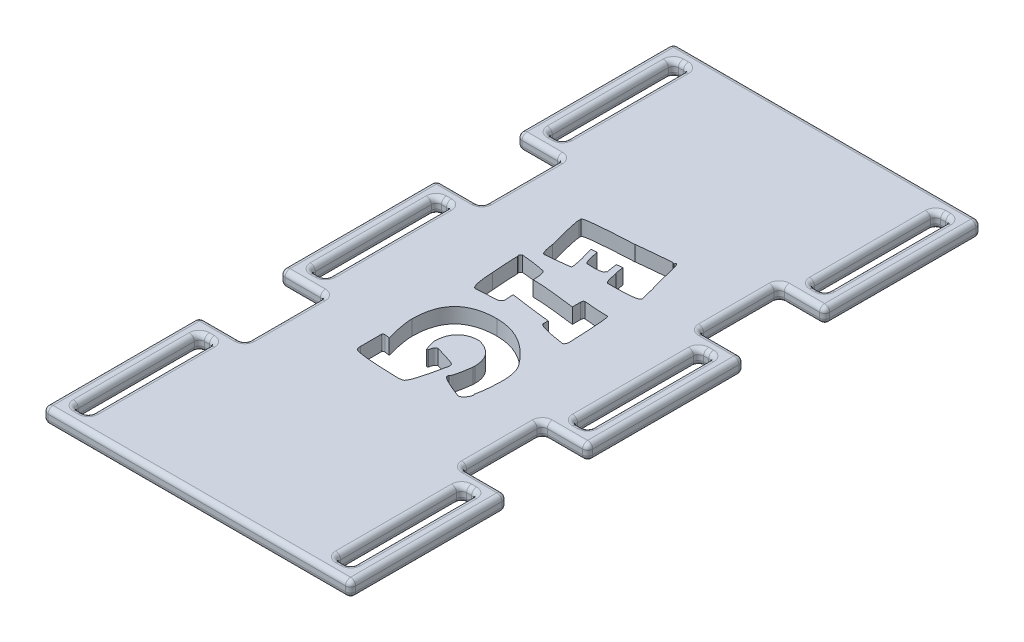
SolidWorks part; units mm, degrees
ref_plane "Front Plane" through (0, 0, 0) normal (0, 0, 1) x (1, 0, 0)
ref_plane "Top Plane" through (0, 0, 0) normal (0, 1, 0) x (1, 0, 0)
ref_plane "Right Plane" through (0, 0, 0) normal (1, 0, 0) x (0, 0, -1)
sketch "Sketch1" plane through (0, 0, 0) normal (0, 1, 0) x (1, 0, 0)
  line L1 (0, 0) -> (43, 0)
  line L2 (0, 0) -> (0, 125)
  line L3 (0, 125) -> (43, 125)
  line L4 (43, 0) -> (43, 125)
extrude "Boss-Extrude2" add sketch "Sketch1" along normal blind 3 contours L3 L4 L1 L2
sketch "Sketch3" plane through (0, 0, 0) normal (0, 1, 0) x (1, 0, 0)
  line L0 (0, 0) -> (0, 125) construction
  line L1 (0, 0) -> (-9, 0)
  line L2 (0, 0) -> (0, 31)
  line L3 (0, 31) -> (-9, 31)
  line L4 (-9, 0) -> (-9, 31)
  line L5 (43, 0) -> (52, 0)
  line L6 (43, 0) -> (43, 31)
  line L7 (43, 31) -> (52, 31)
  line L8 (52, 0) -> (52, 31)
  line L9 (0, 125) -> (-9, 125)
  line L10 (0, 125) -> (0, 94)
  line L11 (0, 94) -> (-9, 94)
  line L12 (-9, 125) -> (-9, 94)
  line L13 (43, 125) -> (52, 125)
  line L14 (43, 125) -> (43, 94)
  line L15 (43, 94) -> (52, 94)
  line L16 (52, 125) -> (52, 94)
  line L17 (0, 78) -> (-9, 78)
  line L18 (0, 78) -> (0, 47)
  line L19 (0, 47) -> (-9, 47)
  line L20 (-9, 78) -> (-9, 47)
  line L21 (43, 0) -> (43, 125) construction
  line L22 (43, 78) -> (52, 78)
  line L23 (43, 78) -> (43, 47)
  line L24 (43, 47) -> (52, 47)
  line L25 (52, 78) -> (52, 47)
  line L27 (-6, 28) -> (-3, 28)
  line L28 (-6, 28) -> (-6, 3)
  line L29 (-6, 3) -> (-3, 3)
  line L30 (-3, 28) -> (-3, 3)
  line L31 (46, 28) -> (49, 28)
  line L32 (46, 28) -> (46, 3)
  line L33 (46, 3) -> (49, 3)
  line L34 (49, 28) -> (49, 3)
  line L35 (46, 122) -> (49, 122)
  line L36 (46, 122) -> (46, 97)
  line L37 (46, 97) -> (49, 97)
  line L38 (49, 122) -> (49, 97)
  line L39 (46, 75) -> (49, 75)
  line L40 (46, 75) -> (46, 50)
  line L41 (46, 50) -> (49, 50)
  line L42 (49, 75) -> (49, 50)
  line L43 (-6, 75) -> (-3, 75)
  line L44 (-6, 75) -> (-6, 50)
  line L45 (-6, 50) -> (-3, 50)
  line L46 (-3, 75) -> (-3, 50)
  line L47 (-6, 122) -> (-3, 122)
  line L48 (-6, 122) -> (-6, 97)
  line L49 (-6, 97) -> (-3, 97)
  line L50 (-3, 122) -> (-3, 97)
  dimension "D1" = 25
  dimension "D2" = 25
  dimension "D3" = 3
  dimension "D4" = 3
  dimension "D5" = 3
  dimension "D6" = 3
  dimension "D7" = 3
  dimension "D8" = 3
  dimension "D9" = 3
  dimension "D10" = 3
  dimension "D11" = 3
  dimension "D12" = 3
  dimension "D13" = 3
  dimension "D14" = 3
  dimension "D15" = 25
  dimension "D16" = 3
  dimension "D17" = 3
  dimension "D18" = 3
  dimension "D19" = 3
  dimension "D20" = 3
  dimension "D21" = 3
  dimension "D22" = 3
  dimension "D23" = 25
  dimension "D24" = 3
  dimension "D25" = 25
  dimension "D26" = 3
  dimension "D27" = 3
  dimension "D28" = 3
  dimension "D29" = 3
  dimension "D30" = 3
  dimension "D31" = 3
  dimension "D32" = 3
  dimension "D33" = 3
  dimension "D34" = 3
  dimension "D35" = 3
  dimension "D36" = 25
  dimension "D37" = 16
  dimension "D38" = 16
  dimension "D39" = 16
  dimension "D40" = 16
extrude "Boss-Extrude3" add sketch "Sketch3" along normal blind 3
fillet "Fillet1" radius 1 132 edges at (47.5, 0, -78) (47.5, 3, -78) (47.5, 0, -94) (47.5, 3, -94) (47.5, 0, -47) (47.5, 3, -47) (47.5, 0, -3) (47.5, 3, -3) (47.5, 0, -28) (47.5, 3, -28) (47.5, 0, -97) (47.5, 3, -97) (47.5, 0, -122) (47.5, 3, -122) (47.5, 0, -50) (47.5, 3, -50) (47.5, 0, -75) (47.5, 3, -75) (-4.5, 0, -97) (-4.5, 3, -97) (-4.5, 0, -122) (-4.5, 3, -122) (-4.5, 0, -50) (-4.5, 3, -50) (-4.5, 0, -75) (-4.5, 3, -75) (-4.5, 0, -3) (-4.5, 3, -3) (-4.5, 0, -28) (-4.5, 3, -28) (-3, 1.5, -122) (-3, 1.5, -97) (-3, 0, -109.5) (-3, 3, -109.5) (49, 1.5, -122) (49, 0, -109.5) (49, 3, -109.5) (49, 1.5, -97) (52, 1.5, -94) (52, 0, -109.5) (52, 3, -109.5) (52, 1.5, -47) (52, 0, -62.5) (52, 3, -62.5) (52, 1.5, -78) (52, 0, -15.5) (52, 3, -15.5) (52, 1.5, -31) (-4.5, 0, -47) (-4.5, 3, -47) (-9, 1.5, -31) (-9, 0, -15.5) (-9, 3, -15.5) (-4.5, 0, -94) (-4.5, 3, -94) (-9, 0, -62.5) (-9, 3, -62.5) (-9, 1.5, -47) (-4.5, 0, -78) (-4.5, 3, -78) (-9, 1.5, -78) (-9, 0, -109.5) (-9, 3, -109.5) (-9, 1.5, -94) (49, 1.5, -75) (49, 0, -62.5) (49, 3, -62.5) (49, 1.5, -50) (49, 1.5, -28) (49, 0, -15.5) (49, 3, -15.5) (49, 1.5, -3) (0, 1.5, -47) (-3, 1.5, -75) (-3, 0, -62.5) (-3, 3, -62.5) (-3, 1.5, -50) (0, 1.5, -94) (0, 1.5, -78) (43, 1.5, -94) (43, 1.5, -78) (43, 1.5, -47) (46, 1.5, -3) (46, 0, -15.5) (46, 3, -15.5) (46, 1.5, -28) (46, 1.5, -97) (46, 0, -109.5) (46, 3, -109.5) (46, 1.5, -122) (46, 1.5, -50) (46, 0, -62.5) (46, 3, -62.5) (46, 1.5, -75) (-6, 1.5, -97) (-6, 0, -109.5) (-6, 3, -109.5) (-6, 1.5, -122) (-6, 1.5, -50) (-6, 0, -62.5) (-6, 3, -62.5) (-6, 1.5, -75) (52, 1.5, -125) (21.5, 3, -125) (-9, 1.5, -125) (21.5, 0, -125) (-9, 1.5, 0) (21.5, 3, 0) (52, 1.5, 0) (21.5, 0, 0) (-3, 1.5, -28) (-3, 0, -15.5) (-3, 3, -15.5) (-3, 1.5, -3) (-6, 1.5, -3) (-6, 0, -15.5) (-6, 3, -15.5) (-6, 1.5, -28)
sketch "Sketch5" plane through (0, 3, 0) normal (0, 1, 0) x (1, 0, 0)
  line L0 (12.3326, 87.126) -> (12.3326, 36.7954)
sketch "Sketch4" plane through (0, 3, 0) normal (0, 1, 0) x (1, 0, 0)
  text T0 "EIG" font "Otaku Rant" height 20
extrude "Cut-Extrude1" cut sketch "Sketch4" against normal blind 3
